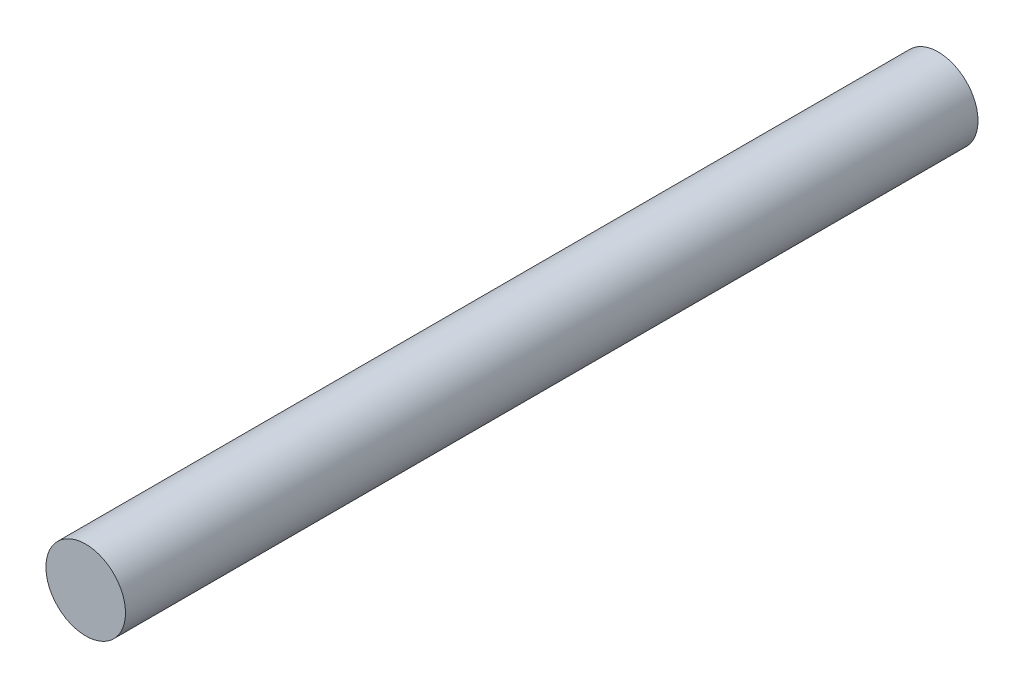
SolidWorks part; units mm, degrees
ref_plane "Front Plane" through (0, 0, 0) normal (0, 0, 1) x (1, 0, 0)
ref_plane "Top Plane" through (0, 0, 0) normal (0, 1, 0) x (1, 0, 0)
ref_plane "Right Plane" through (0, 0, 0) normal (1, 0, 0) x (0, 0, -1)
sketch "Sketch1" plane through (0, 0, 0) normal (0, 0, 1) x (1, 0, 0)
  circle A0 centre (0, 0) radius 3.5
  dimension "D1" = 7
extrude "Boss-Extrude1" add sketch "Sketch1" along normal blind 75
